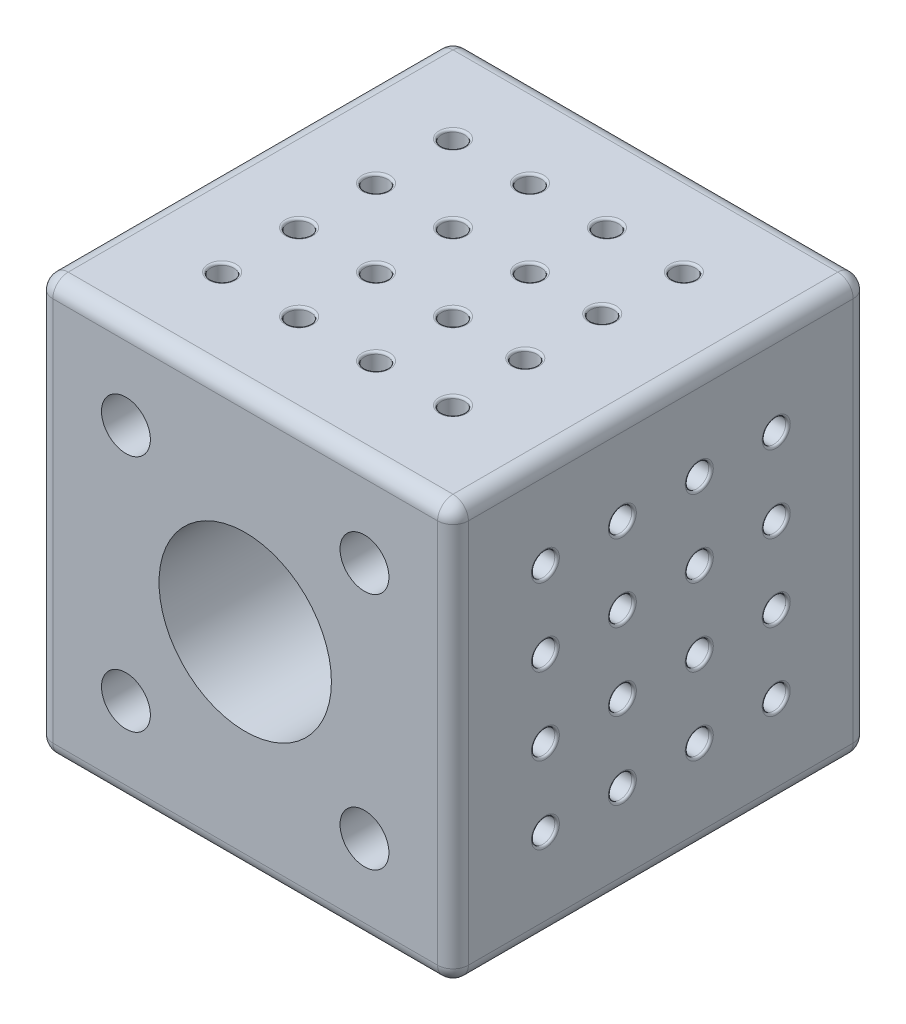
SolidWorks part; units mm, degrees
ref_plane "Front Plane" through (0, 0, 0) normal (0, 0, 1) x (1, 0, 0)
ref_plane "Top Plane" through (0, 0, 0) normal (0, 1, 0) x (1, 0, 0)
ref_plane "Right Plane" through (0, 0, 0) normal (1, 0, 0) x (0, 0, -1)
sketch "Sketch2" plane through (0, 0, 0) normal (0, 0, 1) x (1, 0, 0)
  line L1 (-21.7752, 34.5176) -> (32.2248, 34.5176)
  line L2 (-21.7752, 34.5176) -> (-21.7752, -19.4824)
  line L3 (-21.7752, -19.4824) -> (32.2248, -19.4824)
  line L4 (32.2248, 34.5176) -> (32.2248, -19.4824)
  dimension "D1" = 54
  dimension "D2" = 54
extrude "Boss-Extrude1" add sketch "Sketch2" along normal blind 54 and the other way blind 0.0001
fillet "Fillet1" radius 2 4 edges at (-21.7752, -19.4824, 26.9999) (-21.7752, 34.5176, 26.9999) (32.2248, -19.4824, 26.9999) (32.2248, 34.5176, 26.9999)
fillet "Fillet2" radius 2 16 edges at (31.6391, -18.8966, -0.0001) (-21.1894, -18.8966, -0.0001) (-21.1894, 33.9319, -0.0001) (31.6391, 33.9319, -0.0001) (-21.1894, -18.8966, 54) (-21.1894, 33.9319, 54) (31.6391, 33.9319, 54) (31.6391, -18.8966, 54) (5.2248, 34.5176, -0.0001) (-21.7752, 7.5176, -0.0001) (5.2248, -19.4824, -0.0001) (32.2248, 7.5176, -0.0001) (5.2248, 34.5176, 54) (32.2248, 7.5176, 54) (-21.7752, 7.5176, 54) (5.2248, -19.4824, 54)
sketch "Sketch4" plane through (0, 0, -0.0001) normal (0, 0, -1) x (-1, 0, 0)
  line L0 (19.7752, -17.4824) -> (19.7752, 32.5176) construction
  line L1 (19.7752, 32.5176) -> (-30.2248, 32.5176) construction
  circle A0 centre (-5.2248, 7.5176) radius 11.2
  circle A1 centre (-5.2248, 7.5176) radius 6.1
  dimension "D1" = 22.4
  dimension "D2" = 25
  dimension "D3" = 25
  dimension "D4" = 12.2
extrude "Cut-Extrude1" cut sketch "Sketch4" against normal blind 17 contours A0
sketch "Sketch12" plane through (0, 0, -0.0001) normal (0, 0, -1) x (-1, 0, 0)
  line L0 (-30.2248, 32.5176) -> (-30.2248, -17.4824) construction
  line L1 (-30.2248, -17.4824) -> (19.7752, -17.4824) construction
  line L2 (19.7752, -17.4824) -> (19.7752, 32.5176) construction
  circle A0 centre (-20.7248, 23.0176) radius 6.2
  circle A1 centre (10.2752, 23.0176) radius 6.2
  circle A2 centre (-20.7248, -7.9824) radius 6.2
  circle A3 centre (10.2752, -7.9824) radius 6.2
  dimension "D1" = 12.4
  dimension "D2" = 12.4
  dimension "D4" = 9.5
  dimension "D5" = 12.4
  dimension "D6" = 9.5
  dimension "D7" = 12.4
  dimension "D3" = 31
  dimension "D8" = 31
  dimension "D9" = 31
  dimension "D10" = 31
  dimension "D12" = 9.5
extrude "Cut-Extrude2" cut sketch "Sketch12" against normal blind 33.5
sketch "Sketch13" plane through (0, 0, 33.4999) normal (0, 0, -1) x (-1, 0, 0)
  circle A0 centre (-20.7248, 23.0176) radius 3.175
  circle A1 centre (10.2752, 23.0176) radius 3.175
  circle A2 centre (10.2752, -7.9824) radius 3.175
  circle A3 centre (-20.7248, -7.9824) radius 3.175
  dimension "D1" = 6.35
  dimension "D2" = 6.35
  dimension "D3" = 6.35
  dimension "D4" = 6.35
extrude "Cut-Extrude3" cut sketch "Sketch13" against normal through all
sketch "Sketch14" plane through (0, 0, 16.9999) normal (0, 0, -1) x (-1, 0, 0)
  line L0 (-5.2248, 7.5176) -> (-5.2248, 18.7176) construction
  line L1 (-5.2248, 18.7176) -> (-5.2248, -3.6824) construction
  line L2 (-5.2248, -3.6824) -> (-5.2248, 7.5176) construction
  line L3 (-5.2248, 7.5176) -> (-16.4248, 7.5176) construction
  line L4 (-16.4248, 7.5176) -> (5.9752, 7.5176) construction
  circle A0 centre (-5.2248, 7.5176) radius 11.2 construction
  circle A1 centre (-5.2248, 7.5176) radius 11.2 construction
sketch "Sketch15" plane through (0, 0, 16.9999) normal (0, 0, -1) x (-1, 0, 0)
  line L0 (-5.2248, 7.5176) -> (-5.2248, 18.7176) construction
  line L1 (-5.2248, 7.5176) -> (-16.4248, 7.5176) construction
  line L2 (-5.2248, 18.7176) -> (-5.2248, -3.6824) construction
  line L3 (-16.4248, 7.5176) -> (5.9752, 7.5176) construction
  circle A0 centre (-5.2248, 15.3176) radius 1.5
  circle A1 centre (-13.4248, 7.5176) radius 1.5
  circle A2 centre (-5.2248, -0.6824) radius 1.5
  circle A3 centre (2.5752, 7.5176) radius 1.5
  dimension "D1" = 3
  dimension "D2" = 3
  dimension "D3" = 3
  dimension "D4" = 3
  dimension "D5" = 16
  dimension "D6" = 16
  dimension "D7" = 3
  dimension "D8" = 3
extrude "Cut-Extrude4" cut sketch "Sketch15" against normal through all
sketch "Sketch16" plane through (0, 0, 16.9999) normal (0, 0, -1) x (-1, 0, 0)
  circle A0 centre (-5.2248, 7.5176) radius 6.1
  dimension "D1" = 12.2
extrude "Cut-Extrude5" cut sketch "Sketch16" against normal through all
sketch "Sketch17" plane through (0, 0, 54) normal (0, 0, 1) x (1, 0, 0)
  circle A0 centre (5.2248, 7.5176) radius 11.2
  dimension "D1" = 22.4
extrude "Cut-Extrude6" cut sketch "Sketch17" against normal blind 18
sketch "Sketch18" plane through (0, 0, 16.9999) normal (0, 0, -1) x (-1, 0, 0)
  circle A1 centre (-5.2248, 7.5176) radius 11.1
extrude "Cut-Extrude7" cut sketch "Sketch18" against normal blind 1
sketch "Sketch19" plane through (0, 34.5176, 0) normal (0, 1, 0) x (1, 0, 0)
  line L0 (30.2248, -1.9999) -> (-19.7752, -1.9999) construction
  line L1 (-19.7752, -1.9999) -> (-19.7752, -52) construction
  line L3 (30.2248, -52) -> (30.2248, -1.9999) construction
  line L4 (-19.7752, -52) -> (30.2248, -52) construction
  circle A0 centre (-9.7752, -11.9999) radius 1.5
  circle A1 centre (0.2248, -11.9999) radius 1.5
  circle A2 centre (10.2248, -11.9999) radius 1.5
  circle A3 centre (20.2248, -11.9999) radius 1.5
  circle A4 centre (-9.7752, -21.9999) radius 1.5
  circle A5 centre (0.2248, -21.9999) radius 1.5
  circle A6 centre (10.2248, -21.9999) radius 1.5
  circle A7 centre (19.61, -21.9999) radius 1.5
  circle A8 centre (-9.7752, -31.9999) radius 1.5
  circle A9 centre (0.2248, -31.9999) radius 1.5
  circle A10 centre (10.2248, -31.9999) radius 1.5
  circle A11 centre (19.61, -31.9999) radius 1.5
  circle A12 centre (-9.7752, -41.9999) radius 1.5
  circle A13 centre (0.2248, -41.9999) radius 1.5
  circle A14 centre (10.2248, -42) radius 1.5
  circle A15 centre (20.2248, -42) radius 1.5
  dimension "D1" = 3
  dimension "D2" = 10
  dimension "D3" = 10
  dimension "D4" = 3
  dimension "D6" = 3
  dimension "D8" = 3
  dimension "D12" = 3
  dimension "D14" = 3
  dimension "D17" = 3
  dimension "D18" = 3
  dimension "D20" = 3
  dimension "D21" = 3
  dimension "D22" = 3
  dimension "D23" = 3
  dimension "D24" = 3
  dimension "D28" = 3
  dimension "D29" = 3
  dimension "D30" = 3
  dimension "D5" = 10
  dimension "D7" = 10
  dimension "D9" = 10
  dimension "D10" = 10
  dimension "D11" = 10
  dimension "D13" = 10
  dimension "D15" = 10
  dimension "D16" = 10
  dimension "D19" = 10
  dimension "D25" = 10
  dimension "D26" = 10
  dimension "D27" = 10.0001
  dimension "D31" = 10
  dimension "D32" = 10
  dimension "D33" = 10
extrude "Cut-Extrude8" cut sketch "Sketch19" against normal blind 4
sketch "Sketch21" plane through (32.2248, 0, 0) normal (1, 0, 0) x (0, -1, 0)
  line L2 (-32.5176, -52) -> (17.4824, -52) construction
  line L5 (-32.5176, -1.9999) -> (-32.5176, -52) construction
  line L6 (17.4824, -1.9999) -> (-32.5176, -1.9999) construction
  line L7 (17.4824, -52) -> (17.4824, -1.9999) construction
  circle A0 centre (-22.5176, -12) radius 1.525
  circle A1 centre (-12.5176, -12) radius 1.525
  circle A2 centre (-2.5176, -12) radius 1.525
  circle A3 centre (7.4824, -12) radius 1.525
  circle A4 centre (-22.5176, -22) radius 1.525
  circle A5 centre (-12.5176, -22) radius 1.525
  circle A6 centre (-2.5176, -22) radius 1.525
  circle A7 centre (7.4824, -22) radius 1.525
  circle A8 centre (-22.5176, -32) radius 1.525
  circle A9 centre (-12.5176, -32) radius 1.525
  circle A10 centre (-2.5176, -32) radius 1.525
  circle A11 centre (7.4824, -32) radius 1.525
  circle A12 centre (-22.5176, -42) radius 1.525
  circle A13 centre (-12.5176, -42) radius 1.525
  circle A14 centre (-2.5176, -42) radius 1.525
  circle A15 centre (7.4824, -42) radius 1.525
  dimension "D1" = 3.05
  dimension "D4" = 3.05
  dimension "D6" = 3.05
  dimension "D8" = 3.05
  dimension "D12" = 3.05
  dimension "D14" = 3.05
  dimension "D17" = 3.05
  dimension "D18" = 3.05
  dimension "D20" = 3.05
  dimension "D21" = 3.05
  dimension "D22" = 3.05
  dimension "D23" = 3.05
  dimension "D24" = 3.05
  dimension "D28" = 3.05
  dimension "D29" = 3.05
  dimension "D30" = 3.05
  dimension "D5" = 10
  dimension "D7" = 10
  dimension "D9" = 10
  dimension "D10" = 10
  dimension "D11" = 10
  dimension "D13" = 10
  dimension "D15" = 10
  dimension "D16" = 10
  dimension "D19" = 10
  dimension "D25" = 10
  dimension "D26" = 10
  dimension "D27" = 10.0001
  dimension "D31" = 10
  dimension "D32" = 10
  dimension "D33" = 10
  dimension "D34" = 10
  dimension "D35" = 10
  dimension "D36" = 10
  dimension "D37" = 10
  dimension "D38" = 10.0001
  dimension "D39" = 10
  dimension "D40" = 10
  dimension "D41" = 10
  dimension "D42" = 10
  dimension "D43" = 10
  dimension "D44" = 10
  dimension "D45" = 10
  dimension "D46" = 10.0001
  dimension "D47" = 10
  dimension "D48" = 10
  dimension "D49" = 10
  dimension "D50" = 10
  dimension "D51" = 10
  dimension "D52" = 10
  dimension "D53" = 10
  dimension "D54" = 10
  dimension "D55" = 10
  dimension "D56" = 10.0001
  dimension "D57" = 10
extrude "Cut-Extrude10" cut sketch "Sketch21" against normal blind 4
sketch "Sketch22" plane through (0, -19.4824, 0) normal (0, -1, 0) x (0, 0, 1)
  line L0 (1.9999, 19.7752) -> (1.9999, -30.2248) construction
  line L1 (52, 19.7752) -> (1.9999, 19.7752) construction
  line L2 (52, -30.2248) -> (52, 19.7752) construction
  line L3 (1.9999, -30.2248) -> (52, -30.2248) construction
  circle A0 centre (11.9999, 9.7752) radius 1.5
  circle A1 centre (21.9999, 9.7752) radius 1.525
  circle A2 centre (31.9999, 9.7752) radius 1.5
  circle A3 centre (41.9999, 9.7752) radius 1.525
  circle A4 centre (11.9999, -0.2248) radius 1.525
  circle A5 centre (21.9999, -0.2248) radius 1.5
  circle A6 centre (31.9999, -0.2248) radius 1.525
  circle A7 centre (41.9999, -0.2248) radius 1.5
  circle A8 centre (11.9999, -10.2248) radius 1.5
  circle A9 centre (21.9999, -10.2248) radius 1.525
  circle A10 centre (31.9999, -10.2248) radius 1.5
  circle A11 centre (41.9999, -10.2248) radius 1.525
  circle A12 centre (11.9999, -20.2248) radius 1.525
  circle A13 centre (21.9999, -20.2248) radius 1.5
  circle A14 centre (31.9999, -20.2248) radius 1.525
  circle A15 centre (41.9999, -20.2248) radius 1.5
  dimension "D1" = 3
  dimension "D4" = 3.05
  dimension "D6" = 3
  dimension "D8" = 3.05
  dimension "D12" = 3.05
  dimension "D14" = 3
  dimension "D17" = 3.05
  dimension "D18" = 3
  dimension "D20" = 3
  dimension "D21" = 3.05
  dimension "D22" = 3
  dimension "D23" = 3.05
  dimension "D24" = 3.05
  dimension "D28" = 3
  dimension "D29" = 3.05
  dimension "D30" = 3
  dimension "D5" = 10
  dimension "D7" = 10
  dimension "D9" = 10
  dimension "D10" = 10
  dimension "D11" = 10
  dimension "D13" = 10
  dimension "D15" = 10
  dimension "D16" = 10
  dimension "D19" = 10
  dimension "D25" = 10
  dimension "D26" = 10.0001
  dimension "D27" = 10
  dimension "D31" = 10
  dimension "D32" = 10
  dimension "D33" = 10.0001
  dimension "D34" = 10
  dimension "D35" = 10
  dimension "D36" = 10
  dimension "D37" = 10
  dimension "D38" = 10
  dimension "D40" = 10
  dimension "D41" = 10
  dimension "D42" = 10
  dimension "D43" = 10
  dimension "D44" = 10
  dimension "D45" = 10
  dimension "D47" = 10
  dimension "D50" = 10
  dimension "D51" = 10
  dimension "D52" = 10
  dimension "D53" = 10
  dimension "D54" = 10
  dimension "D55" = 10
extrude "Cut-Extrude11" cut sketch "Sketch22" against normal blind 4
sketch "Sketch25" plane through (-21.7752, 0, 0) normal (-1, 0, 0) x (0, 0, 1)
  line L4 (52, 32.5176) -> (1.9999, 32.5176) construction
  line L5 (1.9999, 32.5176) -> (1.9999, -17.4824) construction
  line L6 (1.9999, -17.4824) -> (52, -17.4824) construction
  line L7 (52, -17.4824) -> (52, 32.5176) construction
  circle A0 centre (11.9999, 22.5176) radius 1.5
  circle A1 centre (21.9999, 22.5176) radius 1.5
  circle A2 centre (31.9999, 22.5176) radius 1.5
  circle A3 centre (41.9999, 22.5176) radius 1.5
  circle A4 centre (11.9999, 12.5176) radius 1.525
  circle A5 centre (21.9999, 12.5176) radius 1.525
  circle A6 centre (31.9999, 12.5176) radius 1.525
  circle A7 centre (41.9999, 12.5176) radius 1.525
  circle A8 centre (11.9999, 2.5176) radius 1.525
  circle A9 centre (21.9999, 2.5176) radius 1.525
  circle A10 centre (31.9999, 2.5176) radius 1.525
  circle A11 centre (41.9999, 2.5176) radius 1.525
  circle A12 centre (11.9999, -7.4824) radius 1.5
  circle A13 centre (21.9999, -7.4824) radius 1.5
  circle A14 centre (31.9999, -7.4824) radius 1.5
  circle A15 centre (41.9999, -7.4824) radius 1.5
  dimension "D1" = 3
  dimension "D4" = 3
  dimension "D6" = 3
  dimension "D8" = 3
  dimension "D12" = 3.05
  dimension "D14" = 3.05
  dimension "D17" = 3.05
  dimension "D18" = 3.05
  dimension "D20" = 3.05
  dimension "D21" = 3.05
  dimension "D22" = 3.05
  dimension "D23" = 3.05
  dimension "D24" = 3
  dimension "D28" = 3
  dimension "D29" = 3
  dimension "D30" = 3
  dimension "D5" = 10
  dimension "D7" = 10
  dimension "D9" = 10
  dimension "D10" = 10
  dimension "D11" = 10
  dimension "D13" = 10
  dimension "D15" = 10
  dimension "D16" = 10
  dimension "D19" = 10
  dimension "D25" = 10
  dimension "D26" = 10
  dimension "D27" = 10
  dimension "D31" = 10
  dimension "D32" = 10
  dimension "D33" = 10.0001
  dimension "D34" = 10
  dimension "D35" = 10
  dimension "D36" = 10
  dimension "D37" = 10
  dimension "D38" = 10
  dimension "D40" = 10
  dimension "D41" = 10
  dimension "D42" = 10
  dimension "D43" = 10
  dimension "D44" = 10
  dimension "D45" = 10
  dimension "D47" = 10
  dimension "D50" = 10
  dimension "D51" = 10
  dimension "D52" = 10
  dimension "D53" = 10
  dimension "D54" = 10
  dimension "D55" = 10
extrude "Cut-Extrude13" cut sketch "Sketch25" against normal blind 4
fillet "Fillet3" radius 0.3 32 edges at (-21.7752, 21.0176, 11.9999) (-17.7752, 21.0176, 11.9999) (-21.7752, -8.9824, 11.9999) (-17.7752, -8.9824, 11.9999) (-21.7752, 0.9926, 41.9999) (-17.7752, 0.9926, 41.9999) (-21.7752, 0.9926, 31.9999) (-17.7752, 0.9926, 31.9999) (-21.7752, 0.9926, 21.9999) (-17.7752, 0.9926, 21.9999) (-21.7752, -8.9824, 21.9999) (-17.7752, -8.9824, 21.9999) (-21.7752, -8.9824, 31.9999) (-17.7752, -8.9824, 31.9999) (-21.7752, -8.9824, 41.9999) (-17.7752, -8.9824, 41.9999) (-21.7752, 10.9926, 21.9999) (-17.7752, 10.9926, 21.9999) (-21.7752, 21.0176, 41.9999) (-17.7752, 21.0176, 41.9999) (-21.7752, 21.0176, 31.9999) (-17.7752, 21.0176, 31.9999) (-21.7752, 21.0176, 21.9999) (-17.7752, 21.0176, 21.9999) (-21.7752, 0.9926, 11.9999) (-17.7752, 0.9926, 11.9999) (-21.7752, 10.9926, 41.9999) (-17.7752, 10.9926, 41.9999) (-21.7752, 10.9926, 31.9999) (-17.7752, 10.9926, 31.9999) (-21.7752, 10.9926, 11.9999) (-17.7752, 10.9926, 11.9999)
fillet "Fillet4" radius 0.3 32 edges at (-9.7752, -19.4824, 10.4999) (-9.7752, -15.4824, 10.4999) (20.2248, -19.4824, 10.4749) (20.2248, -15.4824, 10.4749) (10.2248, -19.4824, 40.4749) (10.2248, -15.4824, 40.4749) (10.2248, -19.4824, 30.4999) (10.2248, -15.4824, 30.4999) (10.2248, -19.4824, 20.4749) (10.2248, -15.4824, 20.4749) (20.2248, -19.4824, 20.4999) (20.2248, -15.4824, 20.4999) (20.2248, -19.4824, 30.4749) (20.2248, -15.4824, 30.4749) (20.2248, -19.4824, 40.4999) (20.2248, -15.4824, 40.4999) (0.2248, -19.4824, 20.4999) (0.2248, -15.4824, 20.4999) (-9.7752, -19.4824, 40.4749) (-9.7752, -15.4824, 40.4749) (-9.7752, -19.4824, 30.4999) (-9.7752, -15.4824, 30.4999) (-9.7752, -19.4824, 20.4749) (-9.7752, -15.4824, 20.4749) (10.2248, -19.4824, 10.4999) (10.2248, -15.4824, 10.4999) (0.2248, -19.4824, 40.4999) (0.2248, -15.4824, 40.4999) (0.2248, -19.4824, 30.4749) (0.2248, -15.4824, 30.4749) (0.2248, -19.4824, 10.4749) (0.2248, -15.4824, 10.4749)
fillet "Fillet5" radius 0.3 32 edges at (32.2248, 22.5176, 10.475) (28.2248, 22.5176, 10.475) (32.2248, 22.5176, 40.475) (28.2248, 22.5176, 40.475) (32.2248, -7.4824, 30.475) (28.2248, -7.4824, 30.475) (32.2248, 2.5176, 30.475) (28.2248, 2.5176, 30.475) (32.2248, 12.5176, 30.475) (28.2248, 12.5176, 30.475) (32.2248, 12.5176, 40.475) (28.2248, 12.5176, 40.475) (32.2248, 2.5176, 40.475) (28.2248, 2.5176, 40.475) (32.2248, -7.4824, 40.475) (28.2248, -7.4824, 40.475) (32.2248, 12.5176, 20.475) (28.2248, 12.5176, 20.475) (32.2248, -7.4824, 10.475) (28.2248, -7.4824, 10.475) (32.2248, 2.5176, 10.475) (28.2248, 2.5176, 10.475) (32.2248, 12.5176, 10.475) (28.2248, 12.5176, 10.475) (32.2248, 22.5176, 30.475) (28.2248, 22.5176, 30.475) (32.2248, -7.4824, 20.475) (28.2248, -7.4824, 20.475) (32.2248, 2.5176, 20.475) (28.2248, 2.5176, 20.475) (32.2248, 22.5176, 20.475) (28.2248, 22.5176, 20.475)
fillet "Fillet6" radius 0.3 32 edges at (-9.7752, 34.5176, 13.4999) (-9.7752, 30.5176, 13.4999) (-9.7752, 34.5176, 43.4999) (-9.7752, 30.5176, 43.4999) (19.61, 34.5176, 33.4999) (19.61, 30.5176, 33.4999) (10.2248, 34.5176, 33.4999) (10.2248, 30.5176, 33.4999) (0.2248, 34.5176, 33.4999) (0.2248, 30.5176, 33.4999) (0.2248, 34.5176, 43.4999) (0.2248, 30.5176, 43.4999) (10.2248, 34.5176, 43.5) (10.2248, 30.5176, 43.5) (20.2248, 34.5176, 43.5) (20.2248, 30.5176, 43.5) (0.2248, 34.5176, 23.4999) (0.2248, 30.5176, 23.4999) (20.2248, 34.5176, 13.4999) (20.2248, 30.5176, 13.4999) (10.2248, 34.5176, 13.4999) (10.2248, 30.5176, 13.4999) (0.2248, 34.5176, 13.4999) (0.2248, 30.5176, 13.4999) (-9.7752, 34.5176, 33.4999) (-9.7752, 30.5176, 33.4999) (19.61, 34.5176, 23.4999) (19.61, 30.5176, 23.4999) (10.2248, 34.5176, 23.4999) (10.2248, 30.5176, 23.4999) (-9.7752, 34.5176, 23.4999) (-9.7752, 30.5176, 23.4999)
